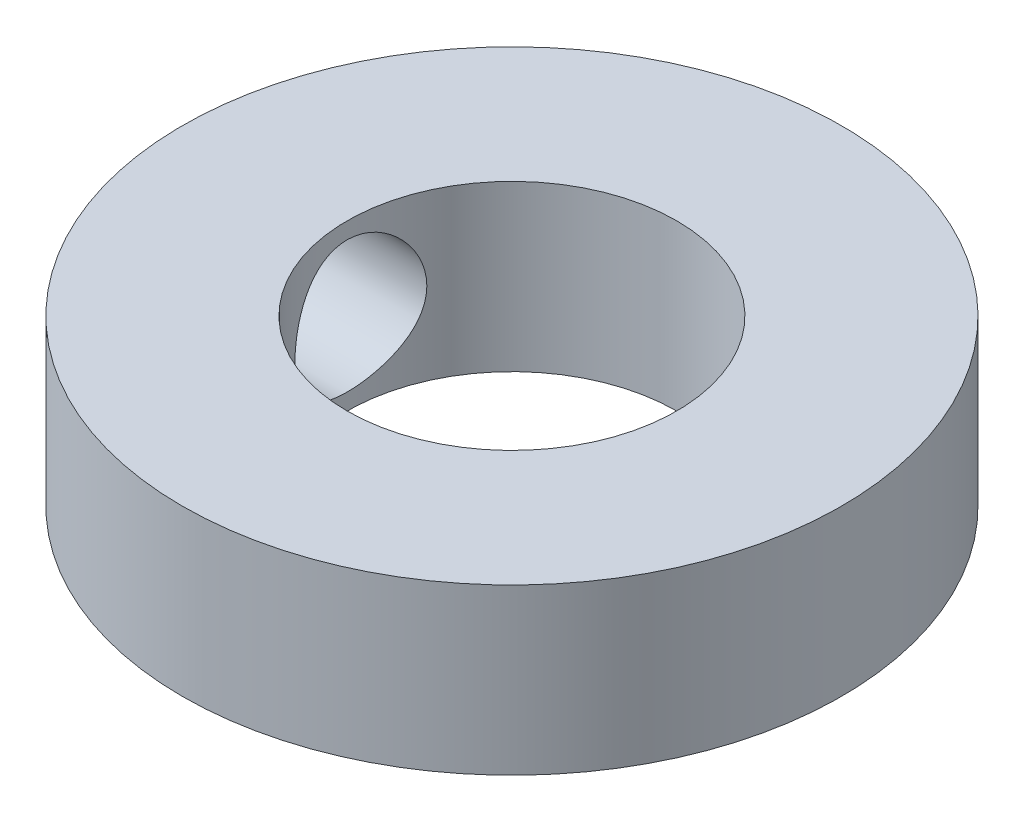
SolidWorks part; units mm, degrees
ref_plane "Front Plane" through (0, 0, 0) normal (0, 0, 1) x (1, 0, 0)
ref_plane "Top Plane" through (0, 0, 0) normal (0, 1, 0) x (1, 0, 0)
ref_plane "Right Plane" through (0, 0, 0) normal (1, 0, 0) x (0, 0, -1)
sketch "Sketch1" plane through (0, 0, 0) normal (0, 1, 0) x (1, 0, 0)
  circle A0 centre (0, 0) radius 3.175
  circle A1 centre (0, 0) radius 6.35
  dimension "D1" = 6.35
  dimension "D2" = 12.7
extrude "Boss-Extrude1" add sketch "Sketch1" along normal blind 3.175
sketch "Sketch2" plane through (0, 0, 0) normal (1, 0, 0) x (0, 0, -1)
  line L0 (6.35, 3.175) -> (-6.35, 3.175) construction
  line L1 (-6.35, 3.175) -> (-6.35, 0) construction
  circle A0 centre (0, 1.5875) radius 1.27
  dimension "D3" = 2.54
  dimension "D1" = 1.5875
  dimension "D2" = 6.35
extrude "Cut-Extrude1" cut sketch "Sketch2" against normal through all contours A0
